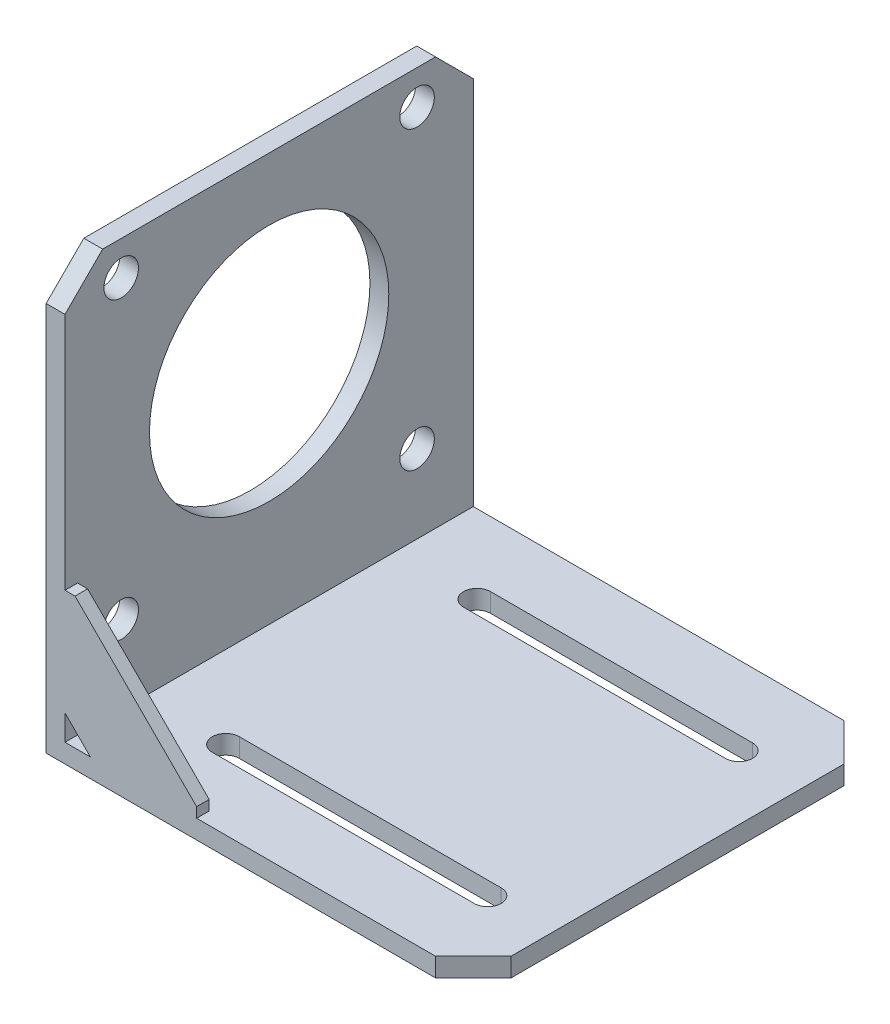
SolidWorks part; units mm, degrees
material "1023 Carbon Steel Sheet (SS)"
ref_plane "Front Plane" through (0, 0, 0) normal (0, 0, 1) x (1, 0, 0)
ref_plane "Top Plane" through (0, 0, 0) normal (0, 1, 0) x (1, 0, 0)
ref_plane "Right Plane" through (0, 0, 0) normal (1, 0, 0) x (0, 0, -1)
sketch "Sketch1" plane through (0, 0, 0) normal (0, 0, 1) x (1, 0, 0)
  line L0 (0, 0) -> (0, 68)
  line L1 (0, 68) -> (3, 68)
  line L2 (3, 68) -> (3, 3)
  line L3 (3, 3) -> (68, 3)
  line L4 (68, 3) -> (68, 0)
  line L5 (68, 0) -> (0, 0)
  dimension "D1" = 3
  dimension "D2" = 3
  dimension "D3" = 65
  dimension "D4" = 65
extrude "Boss-Extrude1" add sketch "Sketch1" along normal blind 65
chamfer "Chamfer1" distance 6 angle 45 4 edges at (68, 1.5, 65) (68, 1.5, 0) (1.5, 68, 0) (1.5, 68, 65)
sketch "Sketch2" plane through (0, 0, 65) normal (0, 0, 1) x (1, 0, 0)
  line L0 (4.6002, 23.9559) -> (23.9559, 4.6002)
  line L3 (23.9559, 3) -> (7.0478, 3)
  line L4 (3, 7.0478) -> (3, 23.9559)
  line L5 (4.6002, 23.9559) -> (3, 23.9559)
  line L6 (23.9559, 4.6002) -> (23.9559, 3)
  line L7 (3, 7.0478) -> (7.0478, 3)
  dimension "D1" = 45
extrude "Boss-Extrude2" add sketch "Sketch2" against normal blind 2
ref_plane "Plane1" through (0, 0, 32.5) normal (0, 0, 1) x (1, 0, 0)
mirror "Mirror1" [suppressed] about plane through (0, 0, 32.5) normal (0, 0, 1)
sketch "Sketch3" plane through (0, 0, 0) normal (-1, 0, 0) x (0, 0, 1)
  line L0 (59, 68) -> (6, 68) construction
  circle A0 centre (32.5, 39) radius 19.05
  circle A1 centre (8.95, 62.55) radius 2.75
  circle A2 centre (56.05, 62.55) radius 2.75
  circle A3 centre (8.95, 15.45) radius 2.75
  circle A4 centre (56.05, 15.45) radius 2.75
  dimension "D2" = 38.1
  dimension "D3" = 5.5
  dimension "D4" = 47.1
  dimension "D5" = 47.1
  dimension "D6" = 47.1
  dimension "D8" = 23.55
  dimension "D1" = 29
  dimension "D7" = 23.55
extrude "Cut-Extrude1" cut sketch "Sketch3" against normal blind 3
sketch "Sketch4" plane through (0, 0, 0) normal (0, -1, 0) x (1, 0, 0)
  line L0 (16.1, 52.5) -> (57.8, 52.5) construction
  line L1 (16.1, 54.65) -> (57.8, 54.65)
  line L2 (16.1, 50.35) -> (57.8, 50.35)
  line L3 (16.1, 12.5) -> (57.8, 12.5) construction
  line L4 (16.1, 14.65) -> (57.8, 14.65)
  line L5 (16.1, 10.35) -> (57.8, 10.35)
  line L6 (0, 65) -> (62, 65) construction
  line L7 (68, 32.5) -> (0, 32.5) construction
  line L8 (68, 59) -> (68, 6) construction
  line L9 (0, 65) -> (0, 0) construction
  arc A0 (16.1, 54.65) -> (16.1, 50.35) centre (16.1, 52.5) ccw
  arc A1 (57.8, 50.35) -> (57.8, 54.65) centre (57.8, 52.5) ccw
  arc A2 (16.1, 14.65) -> (16.1, 10.35) centre (16.1, 12.5) ccw
  arc A3 (57.8, 10.35) -> (57.8, 14.65) centre (57.8, 12.5) ccw
  point P2 (36.95, 52.5)
  point P7 (36.95, 12.5)
  dimension "D1" = 4.3
  dimension "D2" = 41.7
  dimension "D3" = 40
  dimension "D4" = 12.5
  dimension "D5" = 10.2
extrude "Cut-Extrude2" cut sketch "Sketch4" against normal blind 3
